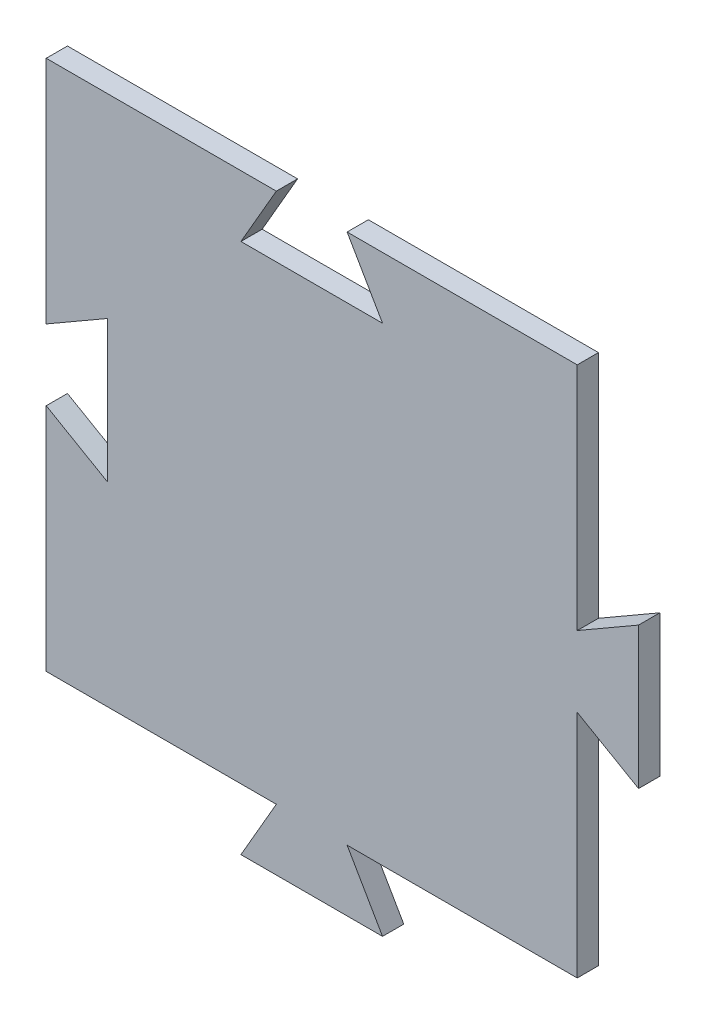
SolidWorks part; units mm, degrees
ref_plane "Plan de face" through (0, 0, 0) normal (0, 0, 1) x (1, 0, 0)
ref_plane "Plan de dessus" through (0, 0, 0) normal (0, 1, 0) x (1, 0, 0)
ref_plane "Plan de droite" through (0, 0, 0) normal (1, 0, 0) x (0, 0, -1)
sketch "Esquisse1" plane through (0, 0, 0) normal (0, 0, 1) x (1, 0, 0)
  line L0 (-89.9481, -21.6084) -> (-49.9481, -21.6084)
  line L1 (-49.9481, -21.6084) -> (-59.9481, -4.2879)
  line L2 (-59.9481, -4.2879) -> (5.0519, -4.2879)
  line L3 (5.0519, -4.2879) -> (5.0519, 60.7121)
  line L4 (5.0519, 60.7121) -> (22.3724, 50.7121)
  line L5 (22.3724, 50.7121) -> (22.3724, 90.7121)
  line L6 (22.3724, 90.7121) -> (5.0519, 80.7121)
  line L7 (5.0519, 80.7121) -> (5.0519, 145.7121)
  line L8 (5.0519, 145.7121) -> (-59.9481, 145.7121)
  line L9 (-59.9481, 145.7121) -> (-49.9481, 128.3916)
  line L10 (-49.9481, 128.3916) -> (-89.9481, 128.3916)
  line L11 (-89.9481, 128.3916) -> (-79.9481, 145.7121)
  line L12 (-79.9481, 145.7121) -> (-144.9481, 145.7121)
  line L13 (-144.9481, 145.7121) -> (-144.9481, 80.7121)
  line L14 (-144.9481, 80.7121) -> (-127.6276, 90.7121)
  line L15 (-127.6276, 90.7121) -> (-127.6276, 50.7121)
  line L16 (-127.6276, 50.7121) -> (-144.9481, 60.7121)
  line L17 (-144.9481, 60.7121) -> (-144.9481, -4.2879)
  line L18 (-144.9481, -4.2879) -> (-79.9481, -4.2879)
  line L19 (-79.9481, -4.2879) -> (-89.9481, -21.6084)
  dimension "D1" = 90
  dimension "D2" = 40
  dimension "D3" = 40
  dimension "D4" = 40
  dimension "D5" = 40
  dimension "D6" = 20
  dimension "D7" = 20
  dimension "D8" = 20
  dimension "D9" = 20
  dimension "D10" = 20
  dimension "D11" = 20
  dimension "D12" = 65
  dimension "D13" = 65
  dimension "D14" = 65
  dimension "D15" = 65
  dimension "D16" = 65
  dimension "D17" = 65
  dimension "D18" = 65
  dimension "D19" = 65
  dimension "D20" = 20
  dimension "D21" = 20
  dimension "D22" = 20
  dimension "D23" = 20
extrude "Boss.-Extru.1" add sketch "Esquisse1" along normal blind 6
